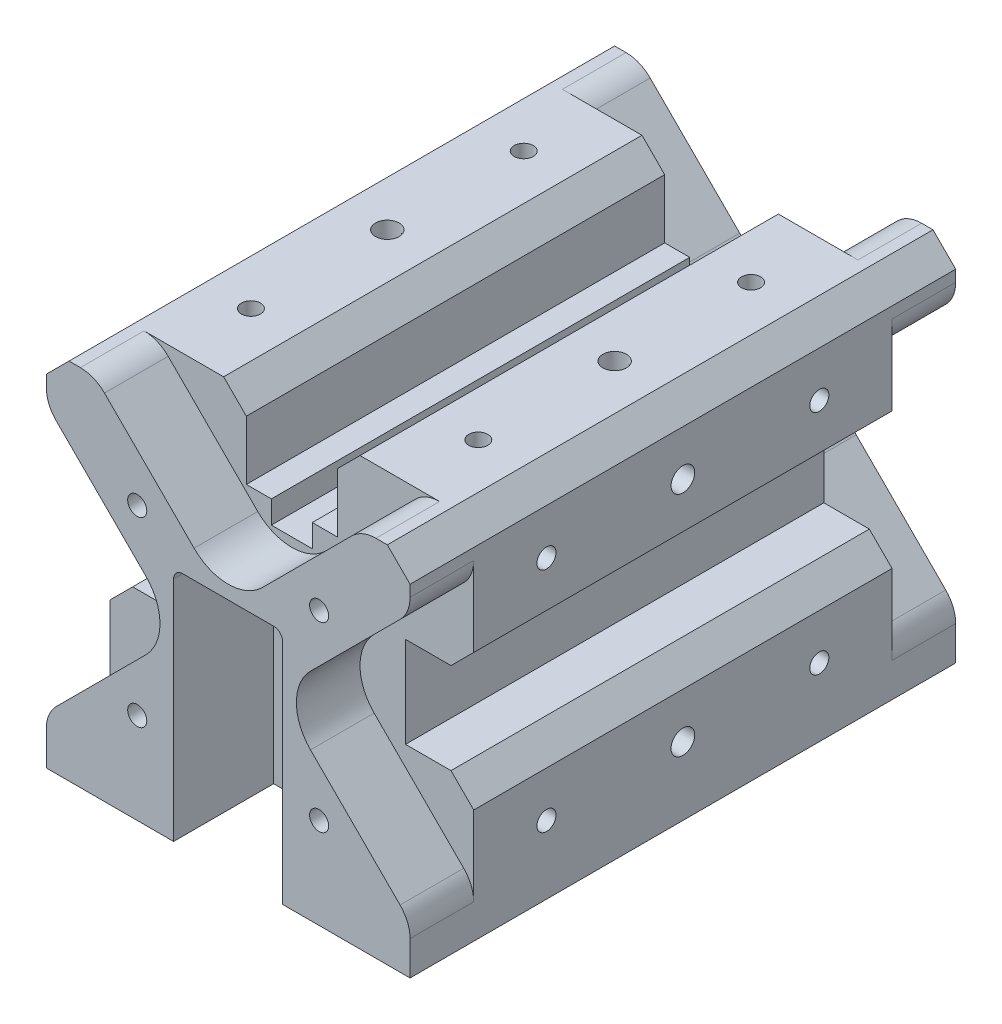
SolidWorks part; units mm, degrees
material "6061 Сплав"
ref_plane "Спереди" through (0, 0, 0) normal (0, 0, 1) x (1, 0, 0)
ref_plane "Сверху" through (0, 0, 0) normal (0, 1, 0) x (1, 0, 0)
ref_plane "Справа" through (0, 0, 0) normal (1, 0, 0) x (0, 0, -1)
sketch "Эскиз7" plane through (0, 0, 0) normal (0, 0, 1) x (1, 0, 0)
  line L0 (-40, 0) -> (40, 0) construction
  line L1 (-40, -40) -> (40, -40)
  line L2 (-40, -40) -> (-40, 40)
  line L3 (-40, 40) -> (40, 40)
  line L4 (40, -40) -> (40, 40)
  point P0 (0, 0)
extrude "Бобышка-Вытянуть2" add sketch "Эскиз7" along normal blind 120
sketch "Эскиз8" plane through (0, 0, 0) normal (0, 0, -1) x (-1, 0, 0)
  line L0 (40, -40) -> (-40, -40) construction
  line L1 (-12, 0) -> (12, 0) construction
  line L2 (-12, -10) -> (-12, 0)
  line L3 (-10, 12) -> (10, 12)
  line L4 (12, -10) -> (12, 0)
  line L5 (-12, -24) -> (12, -24) construction
  line L6 (-12, 0) -> (-12, 10)
  line L7 (12, 0) -> (12, 10)
  line L8 (-12, -10) -> (-12, -24)
  line L9 (-12, -40) -> (12, -40)
  line L10 (12, -10) -> (12, -24)
  line L11 (12, -24) -> (12, -40)
  line L12 (-12, -24) -> (-12, -40)
  arc A0 (12, 10) -> (10, 12) centre (10, 10) ccw
  arc A1 (-10, 12) -> (-12, 10) centre (-10, 10) ccw
  point P0 (0, 0)
  dimension "D3" = 2
  dimension "D1" = 12
  dimension "D2" = 24
  dimension "D5" = 24
extrude "Вырез-Вытянуть2" cut sketch "Эскиз8" against normal blind 22
ref_plane "Плоскость6" through (0, 0, 22) normal (0, 0, -1) x (-1, 0, 0)
sketch "Эскиз10" plane through (0, 0, 22) normal (0, 0, -1) x (-1, 0, 0)
  circle A0 centre (0, 0) radius 2
  circle A1 centre (0, -24) radius 2
sketch "Sketch4" plane through (0, 0, 120) normal (0, 0, 1) x (1, 0, 0)
  line L0 (-40, -40) -> (40, -40) construction
  line L1 (-12, -24) -> (12, -24) construction
  line L2 (-12, 10) -> (-12, 0)
  line L3 (-10, 12) -> (10, 12)
  line L4 (-12, 0) -> (12, 0) construction
  line L5 (12, 10) -> (12, 0)
  line L6 (-12, 0) -> (-12, -24)
  line L7 (12, 0) -> (12, -24)
  line L8 (12, -24) -> (12, -40)
  line L9 (-12, -40) -> (12, -40)
  line L10 (-12, -24) -> (-12, -40)
  arc A0 (-12, 10) -> (-10, 12) centre (-10, 10) cw
  arc A1 (10, 12) -> (12, 10) centre (10, 10) cw
  point P0 (0, 0)
  point P8 (0, 0)
  point P11 (-12, -24)
  point P16 (12, 0)
  point P17 (-12, 0)
  point P18 (12, -24)
  point P19 (-12, -24)
  point P20 (12, -24)
  dimension "D1" = 2
  dimension "D4" = 24
  dimension "D2" = 24
  dimension "D3" = 12
extrude "Cut-Extrude6" cut sketch "Sketch4" against normal blind 22
sketch "Sketch5" plane through (0, 0, 98) normal (0, 0, 1) x (1, 0, 0)
  circle A0 centre (0, 0) radius 2
  circle A1 centre (0, -24) radius 2
extrude "Cut-Extrude8" cut sketch "Sketch5" against normal blind 10
extrude "Cut-Extrude9" cut sketch "Эскиз10" against normal blind 10
sketch "Sketch12" plane through (12, 0, 0) normal (-1, 0, 0) x (0, 0, 1)
  line L0 (120, 0) -> (98, 0)
  line L2 (98, -40) -> (98, 10) construction
sketch "Sketch16" plane through (0, -40, 0) normal (0, -1, 0) x (1, 0, 0)
  point P5 (-34, 113.6)
  point P6 (34, 113.6)
  point P7 (34, 6.4)
  point P8 (-34, 6.4)
  point P10 (10.9, 47.3)
  point P11 (10.9, 6.4)
hole_wizard "M3x0.5 Tapped Hole1" positions "Sketch18" profile "Sketch17" tap size "M3x0.5" standard "ANSI Metric"
sketch "Sketch18" plane through (0, -40, 0) normal (0, -1, 0) x (-1, 0, 0)
  point P12 (-34, -6.4)
  point P305 (-10.886, -47.294)
  point P309 (-34, -113.588)
  point P312 (34.072, -113.588)
  point P315 (34.072, -6.4)
sketch "Sketch17" plane through (34, -40, 6.4) normal (1, 0, 0) x (0, 0, -1)
  line L0 (0, 0) -> (0, 8.2511)
  line L1 (0, 8.2511) -> (1.25, 7.5)
  line L2 (1.25, 7.5) -> (1.25, 0)
  line L5 (1.25, 0) -> (0, 0)
  line L10 (0, 8.2511) -> (-1.25, 7.5) construction
  line L11 (0, -6.35) -> (0, 107.95) construction
  dimension "Tap Drill Dia." = 2.5
  dimension "Tap Drill Depth" = 7.5
  dimension "Drill Angle" = 118
cosmetic thread "Hole Thread1" parameters "D1"=5, "D2"=3
cosmetic thread "Hole Thread2" parameters "D1"=5, "D2"=3
cosmetic thread "Hole Thread4" parameters "D1"=5, "D2"=3
cosmetic thread "Hole Thread5" parameters "D1"=5, "D2"=3
cosmetic thread "Hole Thread6" parameters "D1"=5, "D2"=3
sketch "Sketch19" plane through (0, 0, 120) normal (0, 0, -1) x (-1, 0, 0)
  line L1 (20, -20) -> (-20, -20) construction
  line L2 (20, -20) -> (20, 20) construction
  line L3 (20, 20) -> (-20, 20) construction
  line L4 (-20, -20) -> (-20, 20) construction
  line L5 (20, -20) -> (-20, 20) construction
  line L6 (20, 20) -> (-20, -20) construction
  point P0 (0, 0)
  point P7 (-20, 20)
  point P8 (20, 20)
  point P9 (20, -20)
  point P10 (-20, -20)
sketch "Sketch28" plane through (0, 0, 0) normal (0, 0, -1) x (-1, 0, 0)
  line L1 (-20, -20) -> (20, -20) construction
  line L2 (-20, -20) -> (-20, 20) construction
  line L3 (-20, 20) -> (20, 20) construction
  line L4 (20, -20) -> (20, 20) construction
  line L5 (-20, -20) -> (20, 20) construction
  line L6 (-20, 20) -> (20, -20) construction
  point P0 (0, 0)
  point P1 (0, 0)
  point P2 (0, 0)
  point P7 (-20, 20)
  point P8 (20, 20)
  point P9 (20, -20)
  point P10 (-20, -20)
hole_wizard "M5x0.8 Tapped Hole2" positions "Sketch32" profile "Sketch31" tap size "M5x0.8" standard "ANSI Metric"
sketch "Sketch32" plane through (0, 0, 0) normal (0, 0, -1) x (-1, 0, 0)
  point P0 (-20, 20)
  point P3 (20, 20)
  point P6 (20, -20)
  point P9 (-20, -20)
sketch "Sketch31" plane through (20, 20, 0) normal (1, 0, 0) x (0, 1, 0)
  line L0 (0, 0) -> (0, 20.2618)
  line L1 (0, 20.2618) -> (2.1, 19)
  line L2 (2.1, 19) -> (2.1, 0)
  line L5 (2.1, 0) -> (0, 0)
  line L10 (0, 20.2618) -> (-2.1, 19) construction
  line L11 (0, -6.35) -> (0, 107.95) construction
  dimension "Tap Drill Dia." = 4.2
  dimension "Tap Drill Depth" = 19
  dimension "Drill Angle" = 118
cosmetic thread "Hole Thread15" parameters "D1"=15, "D2"=5
cosmetic thread "Hole Thread16" parameters "D1"=15, "D2"=5
cosmetic thread "Hole Thread17" parameters "D1"=15, "D2"=5
cosmetic thread "Hole Thread18" parameters "D1"=15, "D2"=5
sketch "Sketch38" plane through (40, 0, 0) normal (1, 0, 0) x (0, 0, -1)
  line L2 (-90, 25) -> (-30, -25) construction
  line L3 (-30, 25) -> (-90, -25) construction
  line L4 (-90, 25) -> (-90, -25) construction
  line L5 (-90, -25) -> (-30, -25) construction
  line L6 (-30, -25) -> (-30, 25) construction
  line L7 (-30, 25) -> (-90, 25) construction
  point P0 (-90, 25)
  point P1 (-30, 25)
  point P4 (-90, -25)
  point P5 (-30, -25)
  point P14 (-60, 0)
hole_wizard "M5x0.8 Tapped Hole5" positions "Sketch44" profile "Sketch43" tap size "M5x0.8" standard "ANSI Metric"
sketch "Sketch44" plane through (40, 0, 0) normal (1, 0, 0) x (0, 0, -1)
  point P0 (-90, 25)
  point P3 (-30, 25)
  point P6 (-30, -25)
  point P9 (-90, -25)
sketch "Sketch43" plane through (40, 25, 90) normal (0, 1, 0) x (0, 0, -1)
  line L0 (0, 0) -> (0, 13.6618)
  line L1 (0, 13.6618) -> (2.1, 12.4)
  line L2 (2.1, 12.4) -> (2.1, 0)
  line L5 (2.1, 0) -> (0, 0)
  line L10 (0, 13.6618) -> (-2.1, 12.4) construction
  line L11 (0, -6.35) -> (0, 107.95) construction
  dimension "Tap Drill Dia." = 4.2
  dimension "Tap Drill Depth" = 12.4
  dimension "Drill Angle" = 118
cosmetic thread "Hole Thread23" parameters "D1"=10, "D2"=5
cosmetic thread "Hole Thread24" parameters "D1"=10, "D2"=5
cosmetic thread "Hole Thread25" parameters "D1"=10, "D2"=5
cosmetic thread "Hole Thread26" parameters "D1"=10, "D2"=5
sketch "Sketch45" plane through (0, 40, 0) normal (0, 1, 0) x (1, 0, 0)
  line L1 (-25, -90) -> (25, -90) construction
  line L2 (-25, -90) -> (-25, -30) construction
  line L3 (-25, -30) -> (25, -30) construction
  line L4 (25, -90) -> (25, -30) construction
  line L5 (-25, -90) -> (25, -30) construction
  line L6 (-25, -30) -> (25, -90) construction
  point P0 (0, -60)
  point P4 (0, -60)
  point P8 (-25, -30)
  point P9 (25, -30)
  point P10 (25, -90)
  point P11 (-25, -90)
hole_wizard "M5x0.8 Tapped Hole3" positions "Sketch47" profile "Sketch46" tap size "M5x0.8" standard "ANSI Metric"
sketch "Sketch47" plane through (0, 40, 0) normal (0, 1, 0) x (1, 0, 0)
  point P0 (-25, -30)
  point P3 (25, -30)
  point P6 (25, -90)
  point P9 (-25, -90)
sketch "Sketch46" plane through (-25, 40, 30) normal (1, 0, 0) x (0, 0, 1)
  line L0 (0, 0) -> (0, 13.6618)
  line L1 (0, 13.6618) -> (2.1, 12.4)
  line L2 (2.1, 12.4) -> (2.1, 0)
  line L5 (2.1, 0) -> (0, 0)
  line L10 (0, 13.6618) -> (-2.1, 12.4) construction
  line L11 (0, -6.35) -> (0, 107.95) construction
  dimension "Tap Drill Dia." = 4.2
  dimension "Tap Drill Depth" = 12.4
  dimension "Drill Angle" = 118
cosmetic thread "Hole Thread27" parameters "D1"=10, "D2"=5
cosmetic thread "Hole Thread28" parameters "D1"=10, "D2"=5
cosmetic thread "Hole Thread29" parameters "D1"=10, "D2"=5
cosmetic thread "Hole Thread30" parameters "D1"=10, "D2"=5
sketch "Sketch48" plane through (-40, 0, 0) normal (-1, 0, 0) x (0, 0, 1)
  line L0 (30, 25) -> (90, -25) construction
  line L1 (30, -25) -> (90, -25) construction
  line L2 (30, -25) -> (30, 25) construction
  line L3 (30, 25) -> (90, 25) construction
  line L4 (90, -25) -> (90, 25) construction
  line L5 (30, -25) -> (90, 25) construction
  line L6 (30, 25) -> (90, -25) construction
  point P0 (60, 0)
  point P1 (60, 0)
  point P11 (30, 25)
  point P12 (90, 25)
  point P13 (90, -25)
  point P14 (30, -25)
hole_wizard "M5x0.8 Tapped Hole4" positions "Sketch50" profile "Sketch49" tap size "M5x0.8" standard "ANSI Metric"
sketch "Sketch50" plane through (-40, 0, 0) normal (-1, 0, 0) x (0, 0, 1)
  point P0 (30, 25)
  point P3 (90, 25)
  point P6 (90, -25)
  point P9 (30, -25)
sketch "Sketch49" plane through (-40, 25, 30) normal (0, 1, 0) x (0, 0, 1)
  line L0 (0, 0) -> (0, 13.6618)
  line L1 (0, 13.6618) -> (2.1, 12.4)
  line L2 (2.1, 12.4) -> (2.1, 0)
  line L5 (2.1, 0) -> (0, 0)
  line L10 (0, 13.6618) -> (-2.1, 12.4) construction
  line L11 (0, -6.35) -> (0, 107.95) construction
  dimension "Tap Drill Dia." = 4.2
  dimension "Tap Drill Depth" = 12.4
  dimension "Drill Angle" = 118
cosmetic thread "Hole Thread31" parameters "D1"=10, "D2"=5
cosmetic thread "Hole Thread32" parameters "D1"=10, "D2"=5
cosmetic thread "Hole Thread33" parameters "D1"=10, "D2"=5
cosmetic thread "Hole Thread34" parameters "D1"=10, "D2"=5
sketch "Sketch51" plane through (0, 0, 22) normal (0, 0, -1) x (-1, 0, 0)
  line L0 (-11.9408, 0) -> (11.4323, 0) construction
  line L1 (-11.3619, -24) -> (10.9982, -24) construction
  point P0 (-6, 0)
  point P1 (6, 0)
  point P2 (-6, -24)
  point P3 (6, -24)
  point P4 (0, 0)
  point P5 (0, -24)
hole_wizard "M3x0.5 Tapped Hole4" positions "Sketch53" profile "Sketch52" tap size "M3x0.5" standard "ANSI Metric"
sketch "Sketch53" plane through (0, 0, 22) normal (0, 0, -1) x (-1, 0, 0)
  point P0 (6, 0)
  point P3 (-6, 0)
  point P6 (-6, -24)
  point P9 (6, -24)
sketch "Sketch52" plane through (-6, 0, 22) normal (1, 0, 0) x (0, 1, 0)
  line L0 (0, 0) -> (0, 6.2511)
  line L1 (0, 6.2511) -> (1.25, 5.5)
  line L2 (1.25, 5.5) -> (1.25, 0)
  line L5 (1.25, 0) -> (0, 0)
  line L10 (0, 6.2511) -> (-1.25, 5.5) construction
  line L11 (0, -6.35) -> (0, 107.95) construction
  dimension "Tap Drill Dia." = 2.5
  dimension "Tap Drill Depth" = 5.5
  dimension "Drill Angle" = 118
cosmetic thread "Hole Thread35" parameters "D1"=4, "D2"=3
cosmetic thread "Hole Thread36" parameters "D1"=4, "D2"=3
cosmetic thread "Hole Thread37" parameters "D1"=4, "D2"=3
cosmetic thread "Hole Thread38" parameters "D1"=4, "D2"=3
sketch "Sketch54" plane through (0, 0, 98) normal (0, 0, 1) x (1, 0, 0)
  line L0 (-11.8084, 0) -> (11.4541, 0) construction
  line L1 (-11.8084, -24) -> (11.4541, -24) construction
  point P0 (-6, 0)
  point P1 (6, 0)
  point P3 (-6, -24)
  point P5 (6, -24)
  point P11 (0, -24)
hole_wizard "M3x0.5 Tapped Hole5" positions "Sketch56" profile "Sketch55" tap size "M3x0.5" standard "ANSI Metric"
sketch "Sketch56" plane through (0, 0, 98) normal (0, 0, 1) x (1, 0, 0)
  point P0 (6, 0)
  point P3 (-6, 0)
  point P6 (-6, -24)
  point P9 (6, -24)
sketch "Sketch55" plane through (6, 0, 98) normal (1, 0, 0) x (0, -1, 0)
  line L0 (0, 0) -> (0, 6.2511)
  line L1 (0, 6.2511) -> (1.25, 5.5)
  line L2 (1.25, 5.5) -> (1.25, 0)
  line L5 (1.25, 0) -> (0, 0)
  line L10 (0, 6.2511) -> (-1.25, 5.5) construction
  line L11 (0, -6.35) -> (0, 107.95) construction
  dimension "Tap Drill Dia." = 2.5
  dimension "Tap Drill Depth" = 5.5
  dimension "Drill Angle" = 118
cosmetic thread "Hole Thread39" parameters "D1"=4, "D2"=3
cosmetic thread "Hole Thread40" parameters "D1"=4, "D2"=3
cosmetic thread "Hole Thread41" parameters "D1"=4, "D2"=3
cosmetic thread "Hole Thread42" parameters "D1"=4, "D2"=3
sketch "Sketch33" plane through (40, 0, 0) normal (1, 0, 0) x (0, 0, -1)
  line L0 (-120, 0) -> (0, 0) construction
  line L1 (-60, 25.7894) -> (-60, -37.2877) construction
  line L2 (-90, -25) -> (-30, -25) construction
  line L3 (-30, 25) -> (-90, 25) construction
  circle A2 centre (-60, -25) radius 2.6
  circle A3 centre (-60, 25) radius 2.6
  point P5 (-60, 25)
  point P6 (-60, -25)
  point P19 (0, 12.05)
  point P29 (-60, 25)
  point P33 (-60, -25)
sketch "Sketch34" plane through (0, 40, 0) normal (0, 1, 0) x (1, 0, 0)
  line L0 (0, -120) -> (0, 0) construction
  line L1 (26.5752, -60) -> (-34.6112, -60) construction
  line L3 (25, -90) -> (25, -30) construction
  line L4 (-25, -90) -> (-25, -30) construction
  circle A0 centre (-25, -60) radius 2.6
  circle A2 centre (25, -60) radius 2.6
  point P6 (-25, -60)
  point P7 (25, -60)
  point P8 (-3.1635, -60)
  point P9 (25, -60)
  point P14 (-25, -60)
sketch "Sketch35" plane through (-40, 0, 0) normal (-1, 0, 0) x (0, 0, 1)
  line L0 (-60, 0) -> (180, 0) construction
  line L1 (60, -32.4797) -> (60, 32.2685) construction
  line L2 (30, 25) -> (90, 25) construction
  line L3 (90, -25) -> (30, -25) construction
  circle A2 centre (60, -25) radius 2.6
  circle A3 centre (60, 25) radius 2.6
  point P4 (60, 25)
  point P5 (60, -25)
  point P6 (60, 25)
  point P9 (60, -25)
hole_wizard "M5x0.8 Tapped Hole1" positions "Sketch60" profile "Sketch59" tap size "M5x0.8" standard "ANSI Metric"
sketch "Sketch60" plane through (0, 0, 120) normal (0, 0, 1) x (1, 0, 0)
  point P0 (-20, 20)
  point P3 (20, 20)
  point P6 (20, -20)
  point P9 (-20, -20)
sketch "Sketch59" plane through (-20, 20, 120) normal (1, 0, 0) x (0, -1, 0)
  line L0 (0, 0) -> (0, 20.2618)
  line L1 (0, 20.2618) -> (2.1, 19)
  line L2 (2.1, 19) -> (2.1, 0)
  line L5 (2.1, 0) -> (0, 0)
  line L10 (0, 20.2618) -> (-2.1, 19) construction
  line L11 (0, -6.35) -> (0, 107.95) construction
  dimension "Tap Drill Dia." = 4.2
  dimension "Tap Drill Depth" = 19
  dimension "Drill Angle" = 118
cosmetic thread "Hole Thread43" parameters "D1"=15, "D2"=5
cosmetic thread "Hole Thread44" parameters "D1"=15, "D2"=5
cosmetic thread "Hole Thread45" parameters "D1"=15, "D2"=5
cosmetic thread "Hole Thread46" parameters "D1"=15, "D2"=5
extrude "Cut-Extrude16" cut sketch "Sketch33" against normal blind 11 draft 0.573
extrude "Cut-Extrude17" cut sketch "Sketch34" against normal blind 11 draft 0.573
extrude "Cut-Extrude18" cut sketch "Sketch35" against normal blind 11 draft 0.573
sketch "Sketch63" plane through (0, 0, 0) normal (0, 0, -1) x (-1, 0, 0)
  line L0 (-40, 10) -> (-25, 10)
  line L1 (-40, -40) -> (40, -40)
  line L2 (-25, -10) -> (-40, -10)
  line L3 (40, 10) -> (25, 10)
  line L4 (40, 40) -> (10, 40)
  line L5 (25, 40) -> (-25, 40) construction
  line L6 (40, 40) -> (40, 10)
  line L7 (40, -25) -> (40, 25) construction
  line L8 (40, -40) -> (40, -10)
  line L9 (40, 25) -> (40, -25) construction
  line L10 (-40, 40) -> (-10, 40)
  line L12 (-40, -40) -> (-40, -10)
  line L13 (-40, 25) -> (-40, -25) construction
  line L14 (25, 40) -> (-25, 40) construction
  line L15 (-40, 40) -> (-40, 10)
  line L16 (10, 40) -> (10, 22)
  line L18 (-10, 22) -> (-10, 40)
  line L19 (25, -10) -> (40, -10)
  line L24 (-10, 22) -> (10, 22)
  line L28 (25, 10) -> (25, -10)
  line L32 (-25, 10) -> (-25, -10)
extrude "Cut-Extrude19" cut sketch "Sketch63" against normal through all flip side to cut
sketch "Sketch64" plane through (0, 0, 0) normal (0, 0, -1) x (-1, 0, 0)
  line L0 (-27.1967, 37.8033) -> (-37.8033, 27.1967) construction
  line L1 (-37.8033, -27.1967) -> (-32.5, -32.5) construction
  line L2 (37.8033, -27.1967) -> (32.5, -32.5) construction
  line L4 (40, -32.5) -> (40, -40)
  line L5 (-40, 30.026) -> (-40, 40) construction
  line L6 (40, -40) -> (-40, -40)
  line L7 (-40, -40) -> (-40, -32.5)
  line L8 (-40, 32.5) -> (-40, 40)
  line L9 (-7.5, 18.1066) -> (-18.1066, 7.5) construction
  line L10 (-32.5, 32.5) -> (-32.5, -32.5) construction
  line L11 (-40, -40) -> (-40, -32.5) construction
  line L12 (-40, 40) -> (40, 40) construction
  line L13 (40, -40) -> (-40, 40) construction
  line L14 (40, -40) -> (40, 40) construction
  line L15 (-40, 40) -> (-32.5, 40)
  line L16 (-32.5, -32.5) -> (32.5, -32.5) construction
  line L17 (32.5, 40) -> (40, 40)
  line L18 (7.5, 18.1066) -> (18.1066, 7.5) construction
  line L19 (-32.5, 32.5) -> (32.5, 32.5) construction
  line L20 (32.5, -32.5) -> (32.5, 32.5) construction
  line L21 (-40, -40) -> (40, 40) construction
  line L22 (40, 40) -> (40, 32.5)
  line L23 (-32.5, 32.5) -> (32.5, -32.5) construction
  line L24 (-27.1967, 37.8033) -> (-7.5, 18.1066)
  line L25 (7.5, 18.1066) -> (27.1967, 37.8033)
  line L26 (40, 40) -> (-40, -40) construction
  line L27 (-37.8033, 27.1967) -> (-18.1066, 7.5)
  line L28 (-18.1066, -7.5) -> (-37.8033, -27.1967)
  line L30 (-40, 40) -> (40, -40) construction
  line L31 (37.8033, -27.1967) -> (18.1066, -7.5)
  line L32 (18.1066, 7.5) -> (37.8033, 27.1967)
  arc A0 (18.1066, 7.5) -> (18.1066, -7.5) centre (25.6066, 0) ccw
  arc A1 (-37.8033, 27.1967) -> (-40, 32.5) centre (-32.5, 32.5) cw
  arc A2 (27.1967, 37.8033) -> (32.5, 40) centre (32.5, 32.5) cw
  arc A3 (-18.1066, -7.5) -> (-18.1066, 7.5) centre (-25.6066, 0) ccw
  arc A4 (-7.5, 18.1066) -> (7.5, 18.1066) centre (0, 25.6066) ccw
  circle A5 centre (0, 0) radius 15 construction
  arc A6 (40, -32.5) -> (37.8033, -27.1967) centre (32.5, -32.5) ccw
  arc A7 (-37.8033, -27.1967) -> (-40, -32.5) centre (-32.5, -32.5) ccw
  arc A8 (-32.5, 40) -> (-27.1967, 37.8033) centre (-32.5, 32.5) cw
  arc A9 (40, 32.5) -> (37.8033, 27.1967) centre (32.5, 32.5) cw
  point P18 (0, 0)
  point P24 (0, 0)
  point P34 (-32.5, 32.5)
  point P36 (-12.8033, 12.8033)
  point P43 (12.8033, 12.8033)
  dimension "D2" = 65
  dimension "D3" = 7.5
  dimension "D4" = 30
  dimension "D1" = 80
sketch "Sketch65" plane through (0, 0, 120) normal (0, 0, 1) x (1, 0, 0)
  line L0 (-32.5, 40) -> (32.5, 40)
  line L1 (40, 32.5) -> (40, -32.5)
  line L2 (-40, 32.5) -> (-40, -32.5)
  line L16 (20, -20) -> (30, -30) construction
  line L18 (-40, 32.5) -> (-40, 40) construction
  line L22 (-20, -20) -> (-30, -30) construction
  line L28 (-7.5, 18.1066) -> (-18.1066, 7.5) construction
  line L29 (-32.5, 32.5) -> (-32.5, -32.5) construction
  line L31 (-40, -40) -> (-40, -32.5) construction
  line L32 (-40, 40) -> (40, 40) construction
  line L33 (40, -40) -> (-40, 40) construction
  line L34 (40, -40) -> (40, 40) construction
  line L35 (-32.5, -32.5) -> (32.5, -32.5) construction
  line L36 (7.5, 18.1066) -> (18.1066, 7.5) construction
  line L37 (-32.5, 32.5) -> (32.5, 32.5) construction
  line L38 (32.5, -32.5) -> (32.5, 32.5) construction
  line L39 (-40, -40) -> (40, 40) construction
  line L40 (-32.5, 32.5) -> (32.5, -32.5) construction
  line L41 (-27.1967, 37.8033) -> (-7.5, 18.1066)
  line L42 (7.5, 18.1066) -> (27.1967, 37.8033)
  line L43 (40, 40) -> (-40, -40) construction
  line L44 (-37.8033, 27.1967) -> (-18.1066, 7.5)
  line L45 (-18.1066, -7.5) -> (-37.8033, -27.1967)
  line L46 (-40, 40) -> (40, -40) construction
  line L49 (37.8033, -27.1967) -> (18.1066, -7.5)
  line L50 (18.1066, 7.5) -> (37.8033, 27.1967)
  line L52 (29.3934, -40) -> (40, -40) construction
  arc A0 (40, -32.5) -> (37.8033, -27.1967) centre (32.5, -32.5) ccw
  arc A1 (-37.8033, -27.1967) -> (-40, -32.5) centre (-32.5, -32.5) ccw
  arc A2 (40, 32.5) -> (37.8033, 27.1967) centre (32.5, 32.5) cw
  arc A3 (-32.5, 40) -> (-27.1967, 37.8033) centre (-32.5, 32.5) cw
  arc A4 (18.1066, 7.5) -> (18.1066, -7.5) centre (25.6066, 0) ccw
  arc A5 (-37.8033, 27.1967) -> (-40, 32.5) centre (-32.5, 32.5) cw
  arc A6 (27.1967, 37.8033) -> (32.5, 40) centre (32.5, 32.5) cw
  arc A10 (-18.1066, -7.5) -> (-18.1066, 7.5) centre (-25.6066, 0) ccw
  arc A11 (-7.5, 18.1066) -> (7.5, 18.1066) centre (0, 25.6066) ccw
  circle A12 centre (0, 0) radius 15 construction
  point P0 (-20, 20)
  point P5 (20, 20)
  point P10 (20, -20)
  point P15 (-20, -20)
  point P22 (10, 25)
  point P23 (-10, 32.5)
  point P49 (0, 0)
  point P54 (0, 0)
  point P59 (-27.1967, 37.8033)
  point P60 (-37.8033, 27.1967)
  point P63 (-32.5, 32.5)
  point P65 (-12.8033, 12.8033)
  point P70 (12.8033, 12.8033)
  point P90 (-21.8934, 32.5)
  point P91 (-40, 32.5)
  point P93 (-40, -29.3934)
  point P94 (30, -19.3934)
  point P95 (30, 19.3934)
  point P96 (21.8934, 32.5)
  dimension "D7" = 30
  dimension "D4" = 80
  dimension "D5" = 65
  dimension "D6" = 7.5
sketch "Sketch66" [suppressed] plane through (0, -40, 0) normal (0, -1, 0) x (1, 0, 0)
  line L0 (28, 107.176) -> (28, 105)
  line L1 (-12, 105) -> (-28.072, 105)
  line L2 (-28.072, 105) -> (-28.072, 107.176)
  line L3 (-12, 15) -> (-28.072, 15)
  line L4 (12, 98) -> (12, 120) construction
  line L5 (-28.072, 15) -> (-28.072, 12.8)
  line L6 (12.02, 15) -> (28, 15)
  line L7 (28, 15) -> (28, 12.8)
  line L8 (-12, 105) -> (-12, 15)
  line L9 (28, 12.8) -> (28.1225, 13.1566)
  line L10 (28, 105) -> (12, 105)
  line L11 (-12, 98) -> (-12, 120) construction
  line L13 (12, 105) -> (12, 53.694)
  line L14 (28, 107.176) -> (28, 120)
  line L20 (-28.072, 107.176) -> (-28.072, 120)
  line L26 (-28.072, 12.8) -> (-28.072, 0)
  line L32 (28, 12.8) -> (28, 0)
  line L37 (4.886, 40.894) -> (12, 40.894)
  line L38 (4.886, 40.894) -> (4.886, 53.694)
  line L39 (4.886, 53.694) -> (12, 53.694)
  line L40 (12, 40.894) -> (12.02, 15)
  line L41 (28, 120) -> (-28.072, 120)
  line L45 (-28.072, 0) -> (28, 0)
  point P0 (34, 113.588)
  point P6 (-34.072, 113.588)
  point P32 (-34.072, 6.4)
  point P39 (34, 6.4)
  point P46 (10.886, 47.294)
  dimension "D1" = 6
  dimension "D2" = 6
  dimension "D3" = 6
  dimension "D4" = 6
  dimension "D5" = 6
chamfer "Chamfer1" distance 5 angle 45 8 edges at (-40, 10, 60) (40, 10, 60) (40, -10, 60) (-40, -10, 60) (-10, 40, 60) (10, 40, 60) (-40, 40, 60) (40, 40, 60)
sketch "Эскиз11" plane through (0, 0, 120) normal (0, 0, 1) x (1, 0, 0)
  line L0 (-10, 22) -> (10, 22) construction
  line L1 (-4.5, 22) -> (4.5, 22)
  line L2 (-4.5, 22) -> (-4.5, 17)
  line L3 (-4.5, 17) -> (4.5, 17)
  line L4 (4.5, 22) -> (4.5, 17)
  line L7 (4.5, 22) -> (10, 22) construction
  point P8 (0, 22)
extrude "Вырез-Вытянуть3" cut sketch "Эскиз11" against normal through all
extrude "Вырез-Вытянуть4" cut sketch "Sketch65" against normal blind 14
extrude "Вырез-Вытянуть6" cut sketch "Sketch64" against normal blind 14 flip side to cut
